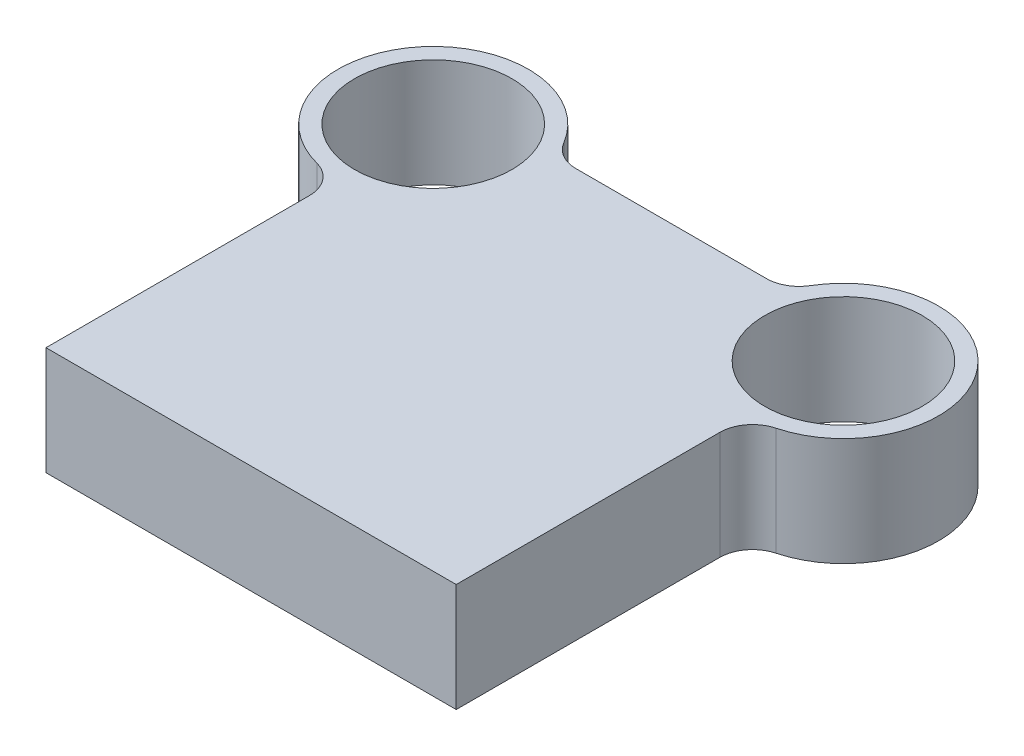
SolidWorks part; units mm, degrees
ref_plane "Front Plane" through (0, 0, 0) normal (0, 0, 1) x (1, 0, 0)
ref_plane "Top Plane" through (0, 0, 0) normal (0, 1, 0) x (1, 0, 0)
ref_plane "Right Plane" through (0, 0, 0) normal (1, 0, 0) x (0, 0, -1)
sketch "Sketch1" plane through (0, 0, 0) normal (0, 1, 0) x (1, 0, 0)
  line L0 (62.5, 0) -> (-62.5, 0)
  line L1 (-62.5, 0) -> (-62.5, 89)
  line L2 (0, 0) -> (0, 128) construction
  line L3 (35.2787, 128) -> (-35.2787, 128)
  line L4 (62.5, 0) -> (62.5, 89)
  arc A0 (-35.2787, 128) -> (-62.5, 89) centre (-62.5, 118) ccw
  circle A1 centre (-62.5, 118) radius 24
  circle A2 centre (62.5, 118) radius 24
  arc A3 (35.2787, 128) -> (62.5, 89) centre (62.5, 118) cw
  point P9 (-133.4133, 89.1683)
  point P10 (-83.6329, 132.6552)
  dimension "D3" = 58
  dimension "D4" = 48
  dimension "D1" = 118
  dimension "D2" = 128
  dimension "D5" = 125
  dimension "D6" = 125
extrude "Boss-Extrude1" add sketch "Sketch1" along normal blind 33
fillet "Fillet1" radius 10 4 edges at (-62.5, 16.5, -89) (-35.2787, 16.5, -128) (35.2787, 16.5, -128) (62.5, 16.5, -89)
